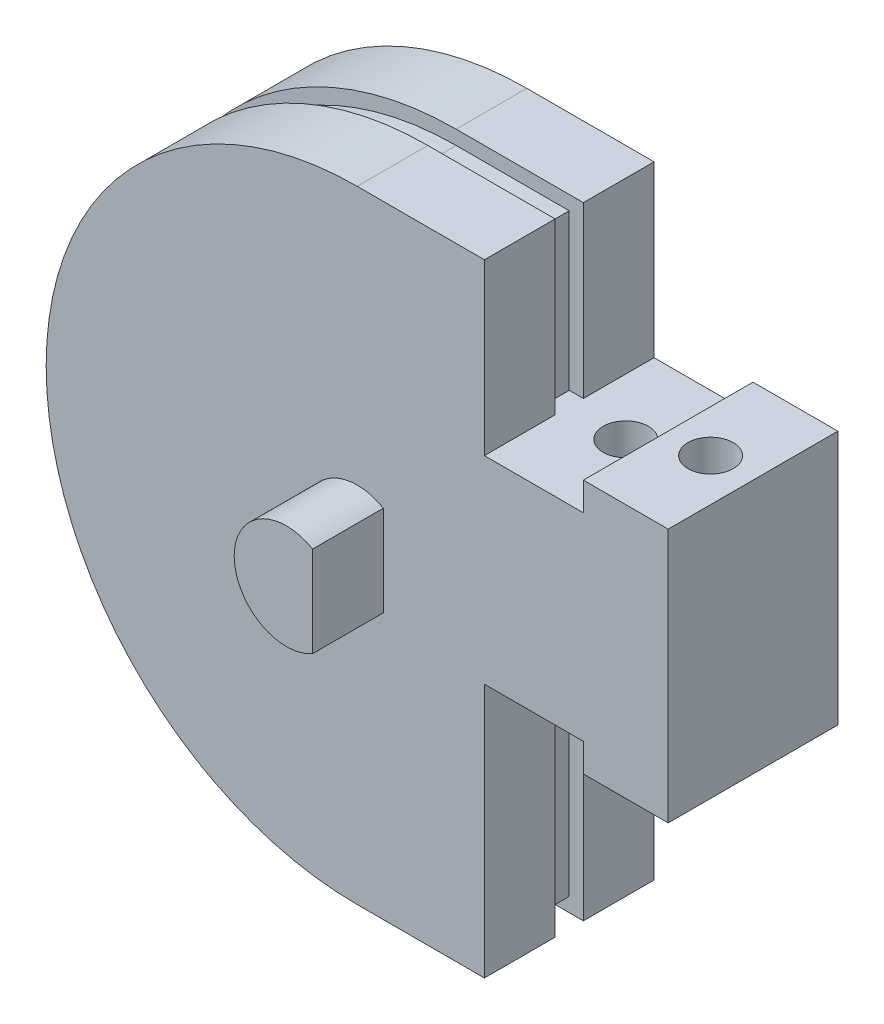
SolidWorks part; units mm, degrees
ref_plane "Front" through (0, 0, 0) normal (0, 0, 1) x (1, 0, 0)
ref_plane "Top" through (0, 0, 0) normal (0, 1, 0) x (1, 0, 0)
ref_plane "Right" through (0, 0, 0) normal (1, 0, 0) x (0, 0, -1)
sketch "Sketch1" plane through (0, 0, 0) normal (0, 0, 1) x (1, 0, 0)
  line L0 (11, 6) -> (11, -3)
  line L1 (0, 11) -> (4.5, 11)
  line L2 (4.5, -2) -> (4.5, -11)
  line L3 (0, -11) -> (4.5, -11)
  line L6 (11, 6) -> (8, 6)
  line L7 (8, 6) -> (8, 5)
  line L9 (8, 5) -> (4.5, 5)
  line L10 (4.5, 5) -> (4.5, 11)
  line L11 (11, -3) -> (8, -3)
  line L12 (8, -3) -> (8, -2)
  line L13 (8, -2) -> (4.5, -2)
  arc A1 (0, 11) -> (0, -11) centre (0, 0) ccw
extrude "Boss-Extrude1" add sketch "Sketch1" along normal blind 6
sketch "Sketch2" plane through (0, 0, 0) normal (0, 1, 0) x (1, 0, 0)
  line L0 (11, -3) -> (9.5, -3) construction
  line L2 (9.5, -3) -> (6.5, -3) construction
  circle A0 centre (6.5, -3) radius 0.8
  circle A1 centre (9.5, -3) radius 0.8
extrude "Cut-Extrude1" cut sketch "Sketch2" against normal through all from offset 10
sketch "Sketch3" plane through (0, 0, 0) normal (0, 0, 1) x (1, 0, 0)
  line L0 (0, 11) -> (4.5, 11)
  line L1 (4.5, -11) -> (4.5, -2)
  line L2 (0, 10.5) -> (4, 10.5)
  line L3 (4, 10.5) -> (4, 5)
  line L4 (0, -11) -> (4.5, -11)
  line L5 (4.5, -2) -> (4, -2)
  line L6 (0, -10.5) -> (4, -10.5)
  line L7 (4, -10.5) -> (4, -2)
  line L9 (4.5, 11) -> (4.5, 5)
  line L10 (4.5, 5) -> (4, 5)
  arc A0 (0, 11) -> (0, -11) centre (0, 0) ccw
  arc A1 (0, 10.5) -> (0, -10.5) centre (0, 0) ccw
extrude "Cut-Extrude2" cut sketch "Sketch3" along normal mid plane 1 from offset 3
sketch "Sketch4" plane through (0, 0, 0) normal (0, 0, 1) x (1, 0, 0)
  line L0 (0, 0) -> (0.925, 0) construction
  line L1 (0.925, 1.6021) -> (0.925, -1.6021)
  arc A0 (0.925, 1.6021) -> (0.925, -1.6021) centre (0, 0) ccw
extrude "Boss-Extrude2" add sketch "Sketch4" along normal blind 2.5 from offset 6
sketch "Sketch5" plane through (0, 0, 0) normal (0, 0, 1) x (1, 0, 0)
  circle A0 centre (0, 0) radius 2.75
extrude "Cut-Extrude3" cut sketch "Sketch5" along normal blind 3.5
